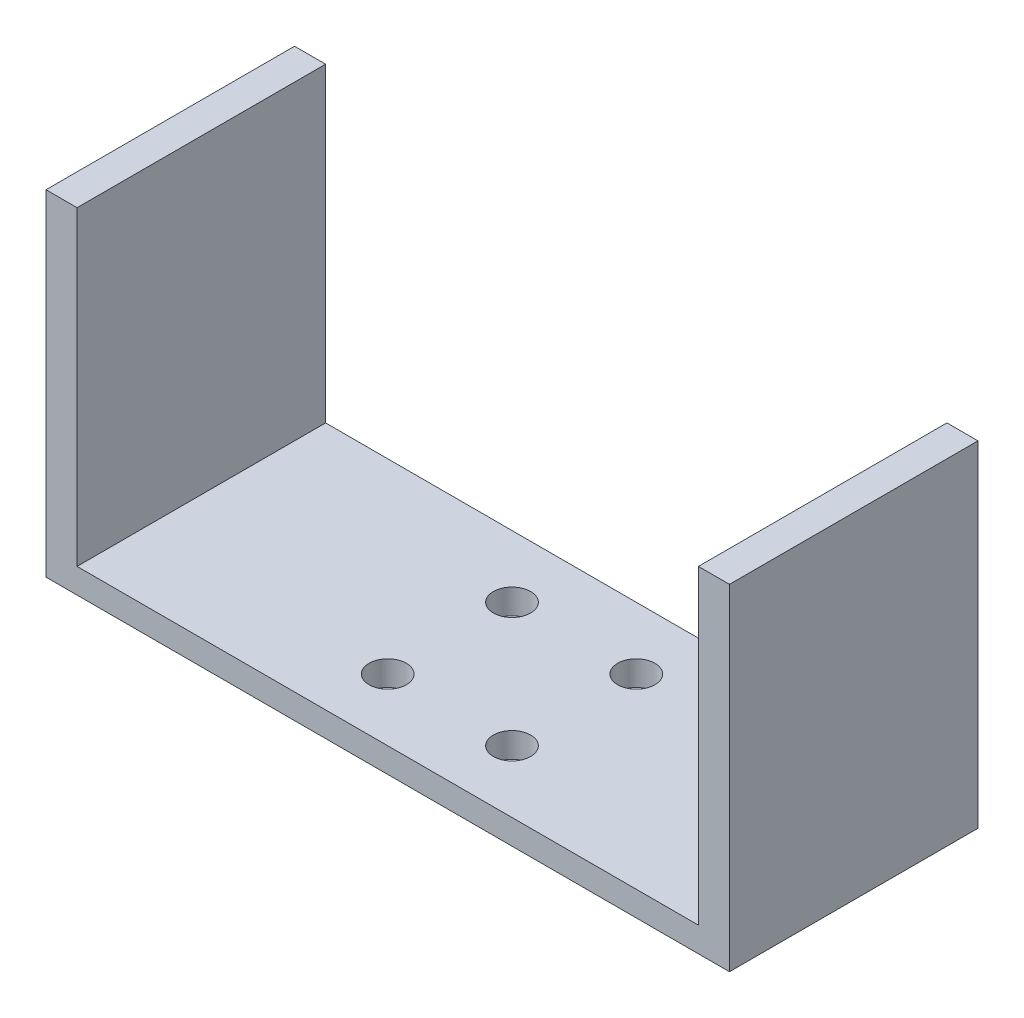
SolidWorks part; units mm, degrees
ref_plane "Front Plane" through (0, 0, 0) normal (0, 0, 1) x (1, 0, 0)
ref_plane "Top Plane" through (0, 0, 0) normal (0, 1, 0) x (1, 0, 0)
ref_plane "Right Plane" through (0, 0, 0) normal (1, 0, 0) x (0, 0, -1)
sketch "Sketch1" plane through (0, 0, 0) normal (0, 1, 0) x (1, 0, 0)
  line L1 (-27.5, 10) -> (27.5, 10)
  line L2 (-27.5, 10) -> (-27.5, -10)
  line L3 (-27.5, -10) -> (27.5, -10)
  line L4 (27.5, 10) -> (27.5, -10)
  line L5 (-27.5, 10) -> (27.5, -10) construction
  line L6 (-27.5, -10) -> (27.5, 10) construction
  point P0 (0, 0)
  dimension "D1" = 55
  dimension "D2" = 20
extrude "Boss-Extrude1" add sketch "Sketch1" along normal blind 2
sketch "Sketch2" plane through (0, 2, 0) normal (0, 1, 0) x (1, 0, 0)
  line L0 (-27.5, -10) -> (27.5, -10) construction
  line L1 (-27.5, 10) -> (-25, 10)
  line L2 (-27.5, 10) -> (-27.5, -10)
  line L3 (-27.5, -10) -> (-25, -10)
  line L4 (-25, 10) -> (-25, -10)
  line L6 (27.5, 10) -> (25, 10)
  line L7 (27.5, 10) -> (27.5, -10)
  line L8 (27.5, -10) -> (25, -10)
  line L9 (25, 10) -> (25, -10)
  dimension "D1" = 2.5
  dimension "D2" = 2.5
extrude "Boss-Extrude2" add sketch "Sketch2" along normal blind 25
sketch "Sketch3" plane through (0, 2, 0) normal (0, 1, 0) x (1, 0, 0)
  line L0 (0, -13.488) -> (0, 13.488) construction
  line L1 (0, 0) -> (-12.6088, 0) construction
  circle A0 centre (5, 5) radius 1.5
  circle A1 centre (-5, 5) radius 1.5
  circle A2 centre (-5, -5) radius 1.5
  circle A3 centre (5, -5) radius 1.5
  dimension "D1" = 3
  dimension "D3" = 5
  dimension "D2" = 5
extrude "Cut-Extrude1" cut sketch "Sketch3" against normal through all
